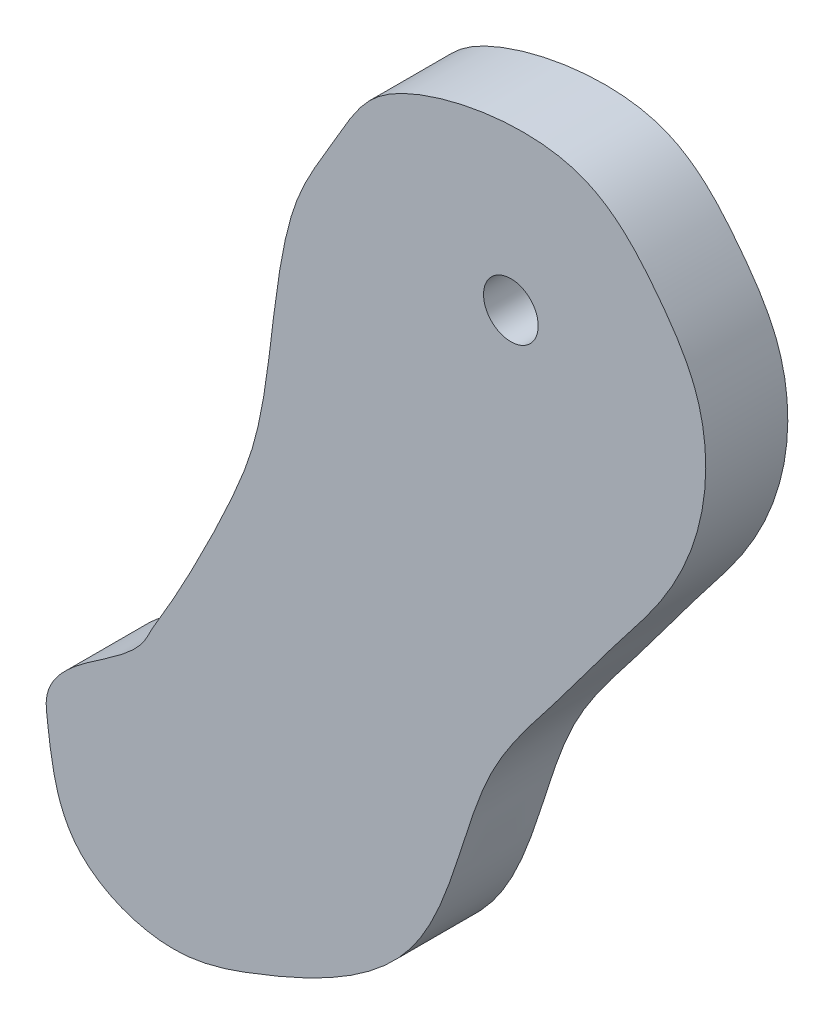
SolidWorks part; units mm, degrees
ref_plane "Спереди" through (0, 0, 0) normal (0, 0, 1) x (1, 0, 0)
ref_plane "Сверху" through (0, 0, 0) normal (0, 1, 0) x (1, 0, 0)
ref_plane "Справа" through (0, 0, 0) normal (1, 0, 0) x (0, 0, -1)
other "Configuration Table"
sketch "Sketch1" plane through (0, 0, 0) normal (0, 0, 1) x (1, 0, 0)
  circle A1 centre (3.0714, 15.9426) radius 1
  spline S0 degree 3 poles (-13.755, -6.5461) (-14.0588, -3.9558) (-10.5195, -1.8472) (-10.1595, -0.7399) (-9.273, 0.4504) (-6.6046, 5.8687) (-5.8643, 8.4353) (-5.2631, 14.9937) (-2.8881, 18.8302) (-1.9561, 21.0714) (5.3929, 22.6269) (8.2701, 19.4445) (10.1888, 16.6288) (10.3461, 13.0124) (8.937, 9.7887) (6.7534, 7.1307) (4.749, 4.3113) (2.0459, 1.0845) (1.136, -2.7938) (-0.883, -7.3396) (-5.1133, -9.3907) (-9.4827, -10.8853) (-13.4151, -9.3478) (-13.755, -6.5461) (-14.0588, -3.9558) (-10.5195, -1.8472) knots -0.091065 -0.04756 -0.004756 0 0.038892 0.095791 0.170637 0.206388 0.248875 0.278359 0.297921 0.348786 0.419462 0.462881 0.494962 0.536061 0.58187 0.614364 0.655354 0.702627 0.75804 0.792049 0.871888 0.908935 0.95244 0.995244 1 1.038892 1.095791 1.170637 only from (-13.9188, -4.9833) to (-13.9188, -4.9833)
  dimension "D1" = 2
extrude "Boss-Extrude1" add sketch "Sketch1" along normal blind 3 contours S0 A1
ref_plane "Plane2" through (0, 0, 0) normal (0, 0, -1) x (-1, 0, 0)
sketch "Sketch2" plane through (0, 0, 0) normal (0, 0, -1) x (-1, 0, 0)
  circle A0 centre (10.3025, -6.5102) radius 1
  circle A1 centre (-3.0714, 15.9426) radius 1 construction
extrude "Boss-Extrude2" add sketch "Sketch2" along normal blind 3 contours A0
equation "\"R small\"= 2"
equation "\"R big\"= 4"
equation "\"width\"= 0.6"
equation "\"border width\"= 1"
equation "\"D1@Sketch1\"=\"R small\""
